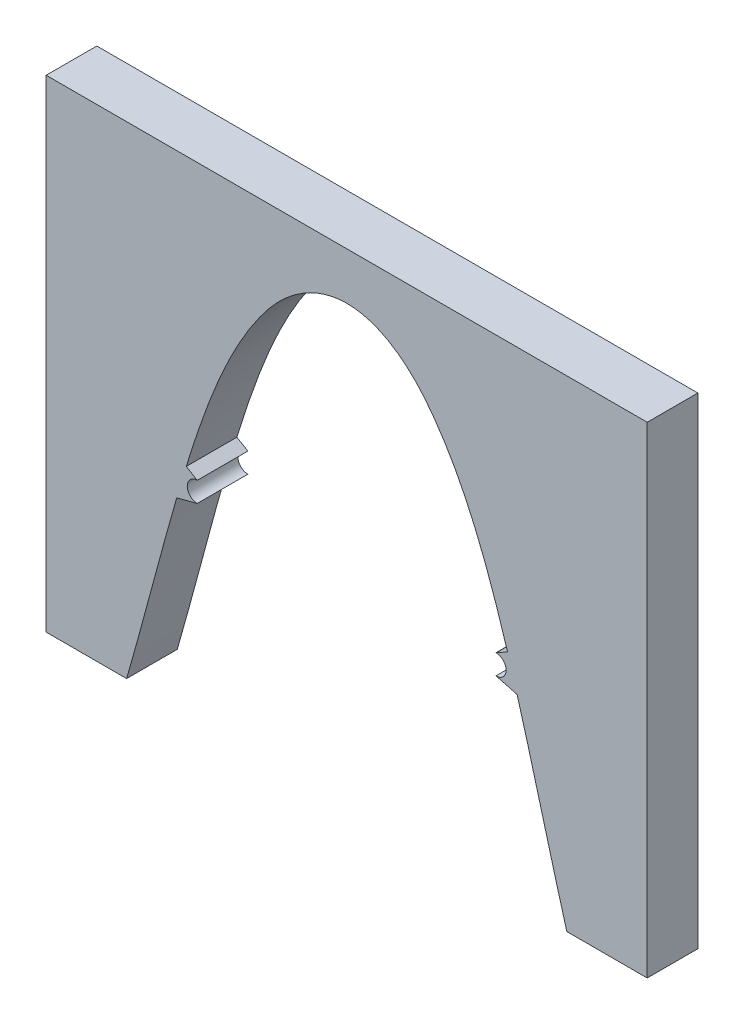
SolidWorks part; units mm, degrees
ref_plane "Front Plane" through (0, 0, 0) normal (0, 0, 1) x (1, 0, 0)
ref_plane "Top Plane" through (0, 0, 0) normal (0, 1, 0) x (1, 0, 0)
ref_plane "Right Plane" through (0, 0, 0) normal (1, 0, 0) x (0, 0, -1)
sketch "Sketch1" plane through (0, 0, 0) normal (0, 0, 1) x (1, 0, 0)
  line L0 (-225.4478, -199.7285) -> (-301.7384, -199.7285)
  line L1 (-301.7384, -199.7285) -> (-301.7384, 257.5935)
  line L2 (-301.7384, 257.5935) -> (268.1726, 257.5935)
  line L3 (268.1726, 257.5935) -> (268.1726, -198.7753)
  line L4 (268.1726, -198.7753) -> (191.9726, -198.7753)
  line L5 (-158.4683, -3.3952) -> (-168.9174, 2.7458)
  line L6 (-158.4683, -22.3972) -> (-177.9619, -27.5814)
  line L7 (-225.4478, -199.7285) -> (191.9726, -198.7753) construction
  line L8 (124.9931, -22.3972) -> (144.8063, -27.6664)
  line L9 (124.9931, -3.3952) -> (135.6919, 2.8925)
  arc A0 (-158.4683, -3.3952) -> (-158.4683, -22.3972) centre (-158.4683, -12.8962) ccw
  arc A1 (124.9931, -22.3972) -> (124.7362, -22.3937) centre (124.9931, -12.8962) cw
  arc A2 (124.7362, -22.3937) -> (124.7362, -3.3986) centre (124.9019, -12.8962) ccw
  arc A3 (124.7362, -3.3986) -> (124.9931, -3.3952) centre (124.9931, -12.8962) cw
  spline S0 degree 3 poles (-177.9619, -27.5814) (-178.686, -30.0813) (-179.4059, -32.5825) (-195.7832, -89.8032) (-209.6436, -145.0523) (-225.4478, -199.7285) knots 0.926685 0.926685 0.926685 0.926685 0.9375 0.9375 1.173999 1.173999 1.173999 1.173999
  spline S1 degree 3 poles (191.9726, -198.7753) (176.3951, -144.7179) (162.6287, -89.958) (146.3818, -33.1253) (145.5965, -30.3949) (144.8063, -27.6664) knots -0.175685 -0.175685 -0.175685 -0.175685 0.0625 0.0625 0.074528 0.074528 0.074528 0.074528
  spline S2 degree 3 poles (135.6919, 2.8925) (135.3147, 4.1166) (134.9361, 5.3402) (132.3688, 13.5999) (130.1307, 20.6169) (125.5245, 34.6004) (123.1575, 41.5673) (115.7974, 62.3677) (110.5481, 76.1018) (101.8439, 96.3808) (98.8035, 103.0865) (92.3776, 116.3642) (88.992, 122.936) (81.7938, 135.9141) (77.9819, 142.3206) (71.869, 151.7771) (69.7654, 154.9036) (66.4983, 159.5502) (65.389, 161.0939) (63.1395, 164.1544) (61.9997, 165.6704) (59.6886, 168.6724) (58.5166, 170.1577) (56.1187, 173.0772) (54.8949, 174.5133) (51.1469, 178.7491) (48.5477, 181.4772) (43.1257, 186.7213) (40.3032, 189.2375) (36.6149, 192.2304) (35.8692, 192.8214) (34.361, 193.9874) (33.5976, 194.5631) (31.2908, 196.2579) (29.7301, 197.3459) (24.9752, 200.4768) (21.7088, 202.3877) (16.6438, 204.9513) (14.9276, 205.755) (11.4353, 207.2526) (9.6581, 207.947) (0.6167, 211.111) (-6.8073, 212.559) (-15.4007, 212.8175) (-16.3611, 212.8271) (-18.2754, 212.8075) (-19.2293, 212.7785) (-22.0813, 212.6349) (-23.9698, 212.4639) (-29.5978, 211.7293) (-33.2999, 210.9462) (-37.8684, 209.6191) (-38.7791, 209.3364) (-40.5948, 208.7367) (-41.5003, 208.4195) (-44.1869, 207.4252) (-45.9453, 206.7033) (-51.132, 204.3781) (-54.4714, 202.6141) (-60.9471, 198.7196) (-64.0836, 196.5892) (-67.8904, 193.721) (-68.6467, 193.1365) (-70.1409, 191.9533) (-70.8797, 191.354) (-73.0719, 189.5338) (-77.36, 185.8042) (-81.3808, 181.8271) (-86.5307, 176.329) (-89.0011, 173.4831) (-92.5563, 169.0751) (-93.7163, 167.5825) (-96.0081, 164.5713) (-97.1383, 163.0512) (-99.369, 159.9834) (-100.4702, 158.4346) (-102.6354, 155.3228) (-103.7003, 153.7586) (-108.9416, 145.8986) (-112.8693, 139.4856) (-120.2912, 126.4558) (-123.7849, 119.8387) (-130.4167, 106.4371) (-133.5547, 99.6527) (-142.5367, 79.096) (-147.9503, 65.1212) (-154.2673, 47.4411) (-155.5079, 43.8944) (-157.9497, 36.7823) (-159.1513, 33.2161) (-162.7024, 22.5025) (-164.9986, 15.3391) (-167.8019, 6.3558) (-168.3613, 4.5512) (-168.9174, 2.7458) knots 0.119569 0.119569 0.119569 0.119569 0.125 0.125 0.15625 0.15625 0.1875 0.1875 0.25 0.25 0.28125 0.28125 0.3125 0.3125 0.34375 0.34375 0.359375 0.359375 0.367187 0.367187 0.375 0.375 0.382812 0.382812 0.390625 0.390625 0.40625 0.40625 0.421875 0.421875 0.425781 0.425781 0.429687 0.429687 0.4375 0.4375 0.453125 0.453125 0.460937 0.460937 0.46875 0.46875 0.5 0.5 0.503906 0.503906 0.507812 0.507812 0.515625 0.515625 0.53125 0.53125 0.535156 0.535156 0.539062 0.539062 0.546875 0.546875 0.5625 0.5625 0.578125 0.578125 0.582031 0.582031 0.585937 0.585937 0.59375 0.609375 0.609375 0.625 0.625 0.632812 0.632812 0.640625 0.640625 0.648437 0.648437 0.65625 0.65625 0.6875 0.6875 0.71875 0.71875 0.75 0.75 0.8125 0.8125 0.828125 0.828125 0.84375 0.84375 0.875 0.875 0.88285 0.88285 0.88285 0.88285
extrude "Boss-Extrude1" add sketch "Sketch1" along normal blind 48.006
